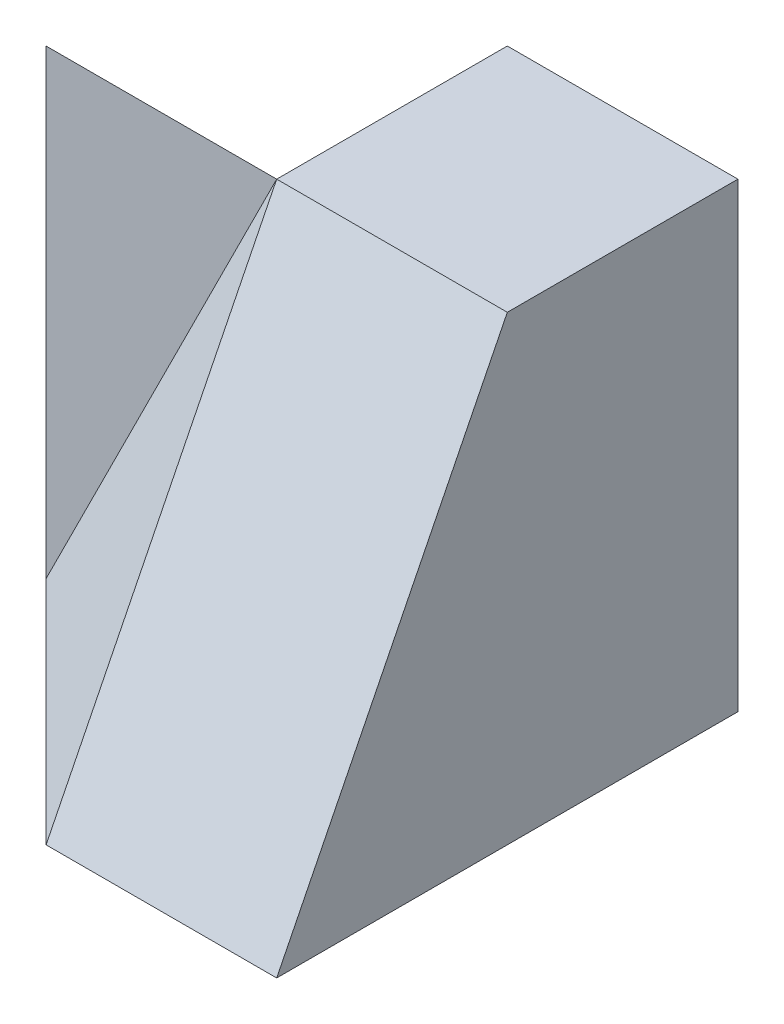
SolidWorks part; units mm, degrees
ref_plane "Front Plane" through (0, 0, 0) normal (0, 0, 1) x (1, 0, 0)
ref_plane "Top Plane" through (0, 0, 0) normal (0, 1, 0) x (1, 0, 0)
ref_plane "Right Plane" through (0, 0, 0) normal (1, 0, 0) x (0, 0, -1)
sketch "Sketch1" plane through (0, 0, 0) normal (0, 0, 1) x (1, 0, 0)
  line L1 (0, 0) -> (40, 0)
  line L2 (0, 0) -> (0, 40)
  line L3 (0, 40) -> (40, 40)
  line L4 (40, 0) -> (40, 40)
  dimension "D1" = 40
  dimension "D2" = 40
extrude "Boss-Extrude1" add sketch "Sketch1" along normal blind 40
sketch "Sketch2" plane through (0, 0, 0) normal (-1, 0, 0) x (0, 0, 1)
  line L0 (40, 0) -> (20, 40)
  line L1 (40, 40) -> (0, 40) construction
  line L2 (20, 40) -> (40, 40)
  line L3 (40, 40) -> (40, 0)
extrude "Cut-Extrude1" cut sketch "Sketch2" against normal blind 40
sketch "Sketch3" plane through (0, 0, 0) normal (0, -1, 0) x (1, 0, 0)
  line L0 (0, 20) -> (20, 40)
  line L1 (0, 40) -> (0, 0) construction
  line L2 (0, 40) -> (40, 40) construction
  line L3 (20, 40) -> (0, 40)
  line L4 (0, 40) -> (0, 20)
extrude "Cut-Extrude2" cut sketch "Sketch3" against normal blind 40
sketch "Sketch4" plane through (0, 0, 0) normal (-1, 0, 0) x (0, 0, 1)
  line L0 (20, 40) -> (0, 20)
  line L1 (0, 40) -> (0, 0) construction
  line L2 (0, 20) -> (0, 40)
  line L3 (0, 40) -> (20, 40)
extrude "Cut-Extrude3" cut sketch "Sketch4" against normal blind 20
ref_plane "Plane1" through (-8.8889, 4.4444, 8.8889) normal (-0.6667, 0.3333, 0.6667) x (0.7454, 0.2981, 0.5963)
sketch "Sketch5" plane through (-8.8889, 4.4444, 8.8889) normal (-0.6667, 0.3333, 0.6667) x (0.7454, 0.2981, 0.5963)
  line L0 (38.7585, 26.8328) -> (38.7585, -17.8885)
  line L1 (38.7585, -17.8885) -> (11.9257, -8.9443)
  line L2 (11.9257, -8.9443) -> (38.7585, 26.8328)
extrude "Cut-Extrude4" cut sketch "Sketch5" along normal blind 20
ref_plane "Plane2" through (0, 0, 20) normal (0, 0, 1) x (1, 0, 0)
sketch "Sketch8" plane through (0, 0, 20) normal (0, 0, 1) x (1, 0, 0)
  line L0 (20, 40) -> (0, 0)
  line L1 (0, 0) -> (0, 40)
  line L2 (0, 40) -> (20, 40)
extrude "Cut-Extrude7" cut sketch "Sketch8" along normal blind 49
